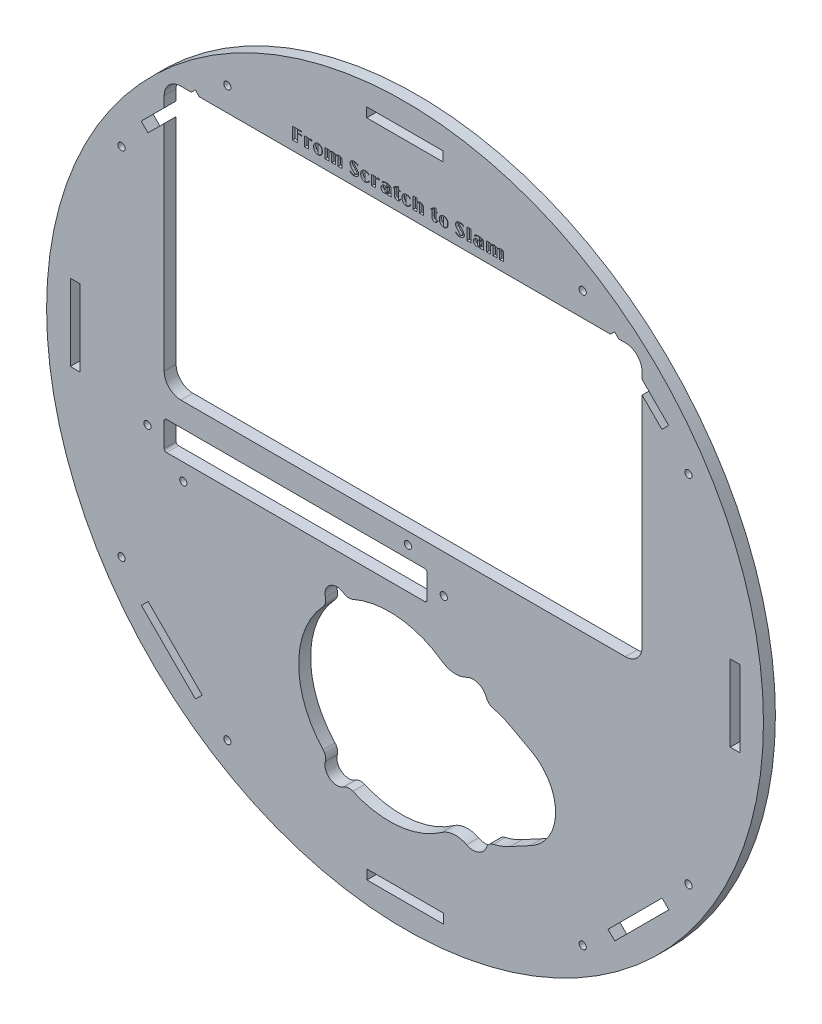
SolidWorks part; units mm, degrees
ref_plane "Plan de face" through (0, 0, 0) normal (0, 0, 1) x (1, 0, 0)
ref_plane "Plan de dessus" through (0, 0, 0) normal (0, 1, 0) x (1, 0, 0)
ref_plane "Plan de droite" through (0, 0, 0) normal (1, 0, 0) x (0, 0, -1)
sketch "Esquisse1" plane through (0, 0, 0) normal (0, 0, 1) x (1, 0, 0)
  circle A0 centre (0, 0) radius 150
extrude "Boss.-Extru.1" add sketch "Esquisse1" along normal blind 5
sketch "Esquisse2" plane through (0, 0, 5) normal (0, 0, 1) x (1, 0, 0)
  line L1 (-75, 30) -> (75, 30)
  line L2 (-75, 30) -> (-75, 80)
  line L3 (-75, 80) -> (75, 80)
  line L4 (75, 30) -> (75, 80)
  dimension "D1" = 50
  dimension "D2" = 150
  dimension "D3" = 75
  dimension "D4" = 80
extrude "Enlèv. mat.-Extru.1" cut sketch "Esquisse2" against normal up to next
sketch "Esquisse3" plane through (0, 0, 5) normal (0, 0, 1) x (1, 0, 0)
  line L0 (-99.2885, 100.18) -> (-99.2885, 3.42) construction
  line L1 (-100.7885, -5.08) -> (99.2115, -5.08)
  line L2 (-100.7885, -5.08) -> (-100.7885, 108.68)
  line L3 (-100.7885, 108.68) -> (99.2115, 108.68)
  line L4 (99.2115, -5.08) -> (99.2115, 108.68)
  line L5 (90.7115, 107.18) -> (-92.2885, 107.18) construction
  line L6 (-92.2885, -3.58) -> (90.7115, -3.58) construction
  line L7 (97.7115, 3.42) -> (97.7115, 100.18) construction
  dimension "D1" = 1.5
  dimension "D2" = 1.5
  dimension "D3" = 1.5
  dimension "D4" = 1.5
extrude "Enlèv. mat.-Extru.2" cut sketch "Esquisse3" against normal up to next
fillet "Congé1" radius 7 4 edges at (99.2115, -5.08, 2.5) (99.2115, 108.68, 2.5) (-100.7885, 108.68, 2.5) (-100.7885, -5.08, 2.5)
sketch "Esquisse5" plane through (0, 0, 5) normal (0, 0, 1) x (1, 0, 0)
  line L0 (0, 0) -> (-35355.3391, -35355.3391) construction
  line L1 (0, 0) -> (35355.3391, -35355.3391) construction
  circle A0 centre (-118.6216, -74.3567) radius 1.5
  circle A1 centre (-118.6216, 74.3567) radius 1.5
  circle A2 centre (-74.3567, -118.6216) radius 1.5
  circle A3 centre (74.3567, -118.6216) radius 1.5
  circle A4 centre (-74.3567, 118.6216) radius 1.5
  circle A5 centre (74.3567, 118.6216) radius 1.5
  circle A6 centre (118.6216, -74.3567) radius 1.5
  circle A7 centre (118.6216, 74.3567) radius 1.5
  dimension "D1" = 140
  dimension "D9" = 140
  dimension "D2" = 140
  dimension "D3" = 140
  dimension "D4" = 140
  dimension "D5" = 31.3
  dimension "D6" = 31.3
  dimension "D7" = 31.3
  dimension "D8" = 31.3
  dimension "D10" = 140
  dimension "D11" = 140
  dimension "D12" = 140
  dimension "D13" = 31.3
  dimension "D14" = 31.3
  dimension "D15" = 31.3
  dimension "D16" = 31.3
extrude "Enlèv. mat.-Extru.5" cut sketch "Esquisse5" against normal up to next
sketch "Esquisse7" plane through (0, 0, 5) normal (0, 0, 1) x (1, 0, 0)
  line L0 (44.0447, -97.9526) -> (52.2614, -93.5324)
  line L1 (44.0447, -54.2724) -> (52.2614, -58.6926)
  arc A0 (-34.2764, -102.0659) -> (-34.2764, -50.159) centre (-6.502, -76.1125) cw
  arc A2 (-21.8322, -41.3276) -> (15.4154, -45.054) centre (-6.502, -76.1125) cw
  arc A4 (-21.8322, -110.8973) -> (15.4154, -107.171) centre (-6.502, -76.1125) ccw
  arc A6 (-33.3337, -105.8261) -> (-25.6927, -111.2487) centre (-28.502, -107.1125) ccw
  arc A7 (-34.2764, -102.0659) -> (-33.3337, -105.8261) centre (-37.199, -104.7969) cw
  arc A9 (-25.6927, -111.2487) -> (-21.8322, -110.8973) centre (-23.4453, -114.5576) cw
  arc A11 (-34.2764, -50.159) -> (-33.3337, -46.3989) centre (-37.199, -47.428) ccw
  arc A13 (-33.3337, -46.3989) -> (-25.6927, -40.9763) centre (-28.502, -45.1125) cw
  arc A15 (-25.6927, -40.9763) -> (-21.8322, -41.3276) centre (-23.4453, -37.6674) ccw
  arc A16 (15.4154, -45.054) -> (25.7542, -45.7766) centre (21.1811, -36.8836) ccw
  arc A18 (25.7542, -45.7766) -> (34.1232, -49.0251) centre (28.498, -51.1125) cw
  arc A20 (34.1232, -49.0251) -> (37.0013, -51.5373) centre (37.8734, -47.6336) ccw
  arc A22 (37.0013, -51.5373) -> (44.0447, -54.2724) centre (31.5112, -76.1125) cw
  arc A24 (52.2614, -58.6926) -> (52.2614, -93.5324) centre (43.498, -76.1125) cw
  arc A26 (44.0447, -97.9526) -> (37.0013, -100.6876) centre (31.5112, -76.1125) cw
  arc A28 (37.0013, -100.6876) -> (34.1232, -103.1998) centre (37.8734, -104.5914) ccw
  arc A30 (34.1232, -103.1998) -> (25.7542, -106.4483) centre (28.498, -101.1125) cw
  arc A32 (15.4154, -107.171) -> (25.7542, -106.4483) centre (21.1811, -115.3414) cw
extrude "Enlèv. mat.-Extru.6" cut sketch "Esquisse7" against normal up to next contours A4 A32 A30 A28 A26 L0 A24 L1 A22 A20 A18 A16 A2 A15 A13 A11 A0 A7 A6 A9
sketch "Esquisse8" plane through (0, 0, 5) normal (0, 0, 1) x (1, 0, 0)
  text T0 "From Scratch to Slam" font "Broadway" height 5
extrude "Enlèv. mat.-Extru.7" cut sketch "Esquisse8" against normal blind 1
sketch "Esquisse10" plane through (0, 0, 5) normal (0, 0, 1) x (1, 0, 0)
  line L0 (92.2115, 108.68) -> (-93.7885, 108.68) construction
  line L1 (-16.0444, 136.08) -> (15.9556, 136.08)
  line L2 (-16.0444, 136.08) -> (-16.0444, 140.08)
  line L3 (-16.0444, 140.08) -> (15.9556, 140.08)
  line L4 (15.9556, 136.08) -> (15.9556, 140.08)
  dimension "D1" = 4
  dimension "D2" = 32
  dimension "D3" = 27.4
extrude "Enlèv. mat.-Extru.8" cut sketch "Esquisse10" against normal up to next (5 mm away)
pattern_circular "Répétition circulaire1" count 8 every 45 about axis through (0, 0, 0) along (0, 0, 1) of "Enlèv. mat.-Extru.8"
sketch "Esquisse11" plane through (0, 0, 5) normal (0, 0, 1) x (1, 0, 0)
  line L0 (-93.7885, -5.08) -> (92.2115, -5.08) construction
  line L1 (-100.7885, -15.08) -> (9.2115, -15.08)
  line L2 (-100.7885, -15.08) -> (-100.7885, -27.08)
  line L3 (-100.7885, -27.08) -> (9.2115, -27.08)
  line L4 (9.2115, -15.08) -> (9.2115, -27.08)
  line L5 (-100.7885, 91.6577) -> (-100.7885, 1.92) construction
  dimension "D1" = 110
  dimension "D2" = 12
  dimension "D3" = 10
  dimension "D4" = 0
extrude "Enlèv. mat.-Extru.9" cut sketch "Esquisse11" against normal up to next
fillet "Congé2" radius 1 4 edges at (-100.7885, -27.08, 2.5) (9.2115, -27.08, 2.5) (9.2115, -15.08, 2.5) (-100.7885, -15.08, 2.5)
sketch "Esquisse12" plane through (0, 0, 5) normal (0, 0, 1) x (1, 0, 0)
  line L0 (-100.7885, -16.08) -> (-100.7885, -26.08) construction
  line L1 (9.2115, -26.08) -> (9.2115, -16.08) construction
  line L2 (8.2115, -15.08) -> (-99.7885, -15.08) construction
  line L3 (-99.7885, -27.08) -> (8.2115, -27.08) construction
  circle A0 centre (-107.7885, -21.08) radius 1.5
  circle A1 centre (16.2115, -21.08) radius 1.5
  circle A2 centre (-92.7885, -34.08) radius 1.5
  circle A3 centre (1.2115, -10.08) radius 1.5
  dimension "D1" = 7
  dimension "D5" = 7
  dimension "D2" = 7
  dimension "D3" = 6
  dimension "D4" = 6
  dimension "D6" = 8
  dimension "D7" = 5
  dimension "D8" = 8
extrude "Enlèv. mat.-Extru.10" cut sketch "Esquisse12" against normal up to next
